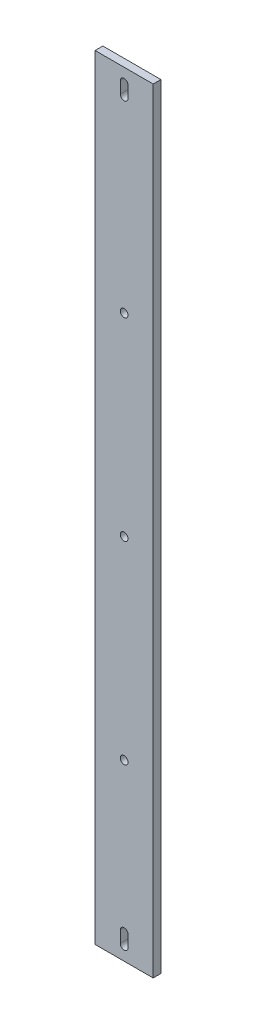
SolidWorks part; units mm, degrees
ref_plane "Plan de face" through (0, 0, 0) normal (0, 0, 1) x (1, 0, 0)
ref_plane "Plan de dessus" through (0, 0, 0) normal (0, 1, 0) x (1, 0, 0)
ref_plane "Plan de droite" through (0, 0, 0) normal (1, 0, 0) x (0, 0, -1)
sketch "Esquisse1" plane through (0, 0, 0) normal (0, 0, 1) x (1, 0, 0)
  line L1 (-52.5897, 52.5) -> (-22.5897, 52.5)
  line L2 (-52.5897, 52.5) -> (-52.5897, -347.5)
  line L3 (-52.5897, -347.5) -> (-22.5897, -347.5)
  line L4 (-22.5897, 52.5) -> (-22.5897, -347.5)
  dimension "D1" = 30
  dimension "D2" = 400
extrude "Boss.-Extru.1" add sketch "Esquisse1" along normal blind 4
sketch "Esquisse2" plane through (0, 0, 4) normal (0, 0, 1) x (1, 0, 0)
  line L0 (-35.5897, 45.5) -> (-35.5897, 39.5)
  line L1 (-39.5897, 45.5) -> (-39.5897, 39.5)
  line L2 (-37.5897, 52.5) -> (-37.5897, -23.8796) construction
  line L3 (-22.5897, 52.5) -> (-52.5897, 52.5) construction
  line L4 (-39.5897, 42.5) -> (-35.5897, 42.5) construction
  line L5 (-37.5897, -347.5) -> (-37.5897, -274.5162) construction
  line L6 (-52.5897, -347.5) -> (-22.5897, -347.5) construction
  line L7 (-35.5897, -334.5) -> (-35.5897, -340.5)
  line L8 (-39.5897, -334.5) -> (-39.5897, -340.5)
  line L9 (-39.5897, -337.5) -> (-35.5897, -337.5) construction
  arc A0 (-35.5897, 45.5) -> (-39.5897, 45.5) centre (-37.5897, 45.5) ccw
  arc A1 (-35.5897, 39.5) -> (-39.5897, 39.5) centre (-37.5897, 39.5) cw
  circle A2 centre (-37.5897, -57.5) radius 2
  arc A3 (-35.5897, -340.5) -> (-39.5897, -340.5) centre (-37.5897, -340.5) cw
  arc A4 (-35.5897, -334.5) -> (-39.5897, -334.5) centre (-37.5897, -334.5) ccw
  circle A5 centre (-37.5897, -257.5) radius 2
  circle A6 centre (-37.5897, -157.5) radius 2
  dimension "D1" = 2
  dimension "D2" = 2
  dimension "D5" = 4
  dimension "D8" = 2
  dimension "D9" = 2
  dimension "D11" = 4
  dimension "D13" = 4
  dimension "D3" = 10
  dimension "D4" = 7
  dimension "D6" = 100
  dimension "D7" = 10
  dimension "D10" = 7
  dimension "D12" = 80
  dimension "D14" = 100
  dimension "D15" = 100
extrude "Enlèv. mat.-Extru.1" cut sketch "Esquisse2" against normal through all
